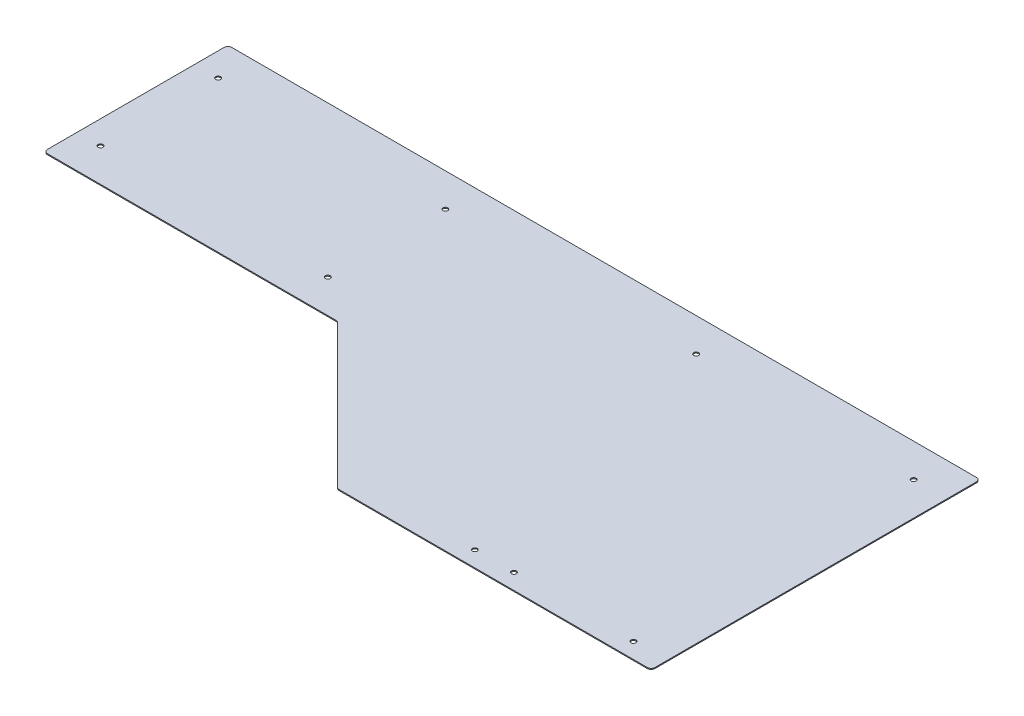
SolidWorks part; units mm, degrees
material "PC High Viscosity"
ref_plane "Front Plane" through (0, 0, 0) normal (0, 0, 1) x (1, 0, 0)
ref_plane "Top Plane" through (0, 0, 0) normal (0, 1, 0) x (1, 0, 0)
ref_plane "Right Plane" through (0, 0, 0) normal (1, 0, 0) x (0, 0, -1)
sketch "Sketch1" plane through (0, 0, 0) normal (0, 1, 0) x (1, 0, 0)
  line L0 (-1219.2, 234.95) -> (-745.5803, 234.95)
  line L1 (-505.3697, 0) -> (0, 0)
  line L2 (-1219.2, 234.95) -> (-1219.2, 533.4)
  line L3 (-1219.2, 533.4) -> (0, 533.4)
  line L4 (0, 0) -> (0, 533.4)
  line L5 (-741.0901, 233.0901) -> (-509.8599, 1.8599)
  arc A0 (-505.3697, 0) -> (-509.8599, 1.8599) centre (-505.3697, 6.35) cw
  arc A1 (-741.0901, 233.0901) -> (-745.5803, 234.95) centre (-745.5803, 228.6) ccw
  point P9 (-508, 0)
  point P12 (-742.95, 234.95)
  dimension "D6" = 6.35
  dimension "D1" = 1219.2
  dimension "D2" = 508
  dimension "D3" = 298.45
  dimension "D4" = 533.4
  dimension "D5" = 476.25
  dimension "D7" = 45
extrude "Boss-Extrude1" add sketch "Sketch1" along normal blind 1.5875
sketch "Sketch2" plane through (0, 1.5875, 0) normal (0, 1, 0) x (1, 0, 0)
  line L0 (0, 0) -> (0, 533.4) construction
  line L1 (0, 533.4) -> (-1219.2, 533.4) construction
  line L2 (-1219.2, 533.4) -> (-1219.2, 234.95) construction
  line L3 (-1219.2, 234.95) -> (-745.5803, 234.95) construction
  line L4 (-505.3697, 0) -> (0, 0) construction
  point P0 (-53.975, 479.425)
  point P1 (-406.4, 479.425)
  point P2 (-1181.1, 479.425)
  point P7 (-1181.1, 288.925)
  point P10 (-812.8, 479.425)
  point P11 (-812.8, 288.925)
  point P12 (-53.975, 25.4)
  point P13 (-311.15, 25.4)
  point P14 (0, 0)
  point P21 (-247.65, 25.4)
  dimension "D1" = 53.975
  dimension "D2" = 53.975
  dimension "D3" = 38.1
  dimension "D4" = 406.4
  dimension "D5" = 53.975
  dimension "32" = 812.8
  dimension "D6" = 25.4
  dimension "D7" = 63.5
  dimension "D8" = 247.65
hole_wizard "5/16 (0.3125) Diameter Hole1" positions "Sketch3" profile "Sketch4" hole size "5/16" standard "ANSI Inch" end condition through all
sketch "Sketch3" plane through (0, 1.5875, 0) normal (0, 1, 0) x (1, 0, 0)
  point P0 (-1181.1, 479.425)
  point P3 (-1181.1, 288.925)
  point P6 (-812.8, 288.925)
  point P9 (-812.8, 479.425)
  point P12 (-406.4, 479.425)
  point P15 (-53.975, 479.425)
  point P18 (-53.975, 25.4)
  point P21 (-247.65, 25.4)
  point P24 (-311.15, 25.4)
sketch "Sketch4" plane through (-1181.1, 1.5875, -479.425) normal (1, 0, 0) x (0, 0, 1)
  line L0 (0, 0) -> (0, 1.5875)
  line L1 (0, 1.5875) -> (3.9688, 1.5875)
  line L2 (3.9688, 1.5875) -> (3.9687, 0)
  line L5 (3.9687, 0) -> (0, 0)
  line L11 (0, -6.35) -> (0, 107.95) construction
  dimension "Thru Hole Dia." = 7.9375
  dimension "Thru Hole Depth" = 1.5875
fillet "Fillet1" radius 6.35 4 edges at (-1219.2, 0.7937, -234.95) (0, 0.7937, -533.4) (0, 0.7937, 0) (-1219.2, 0.7937, -533.4)
